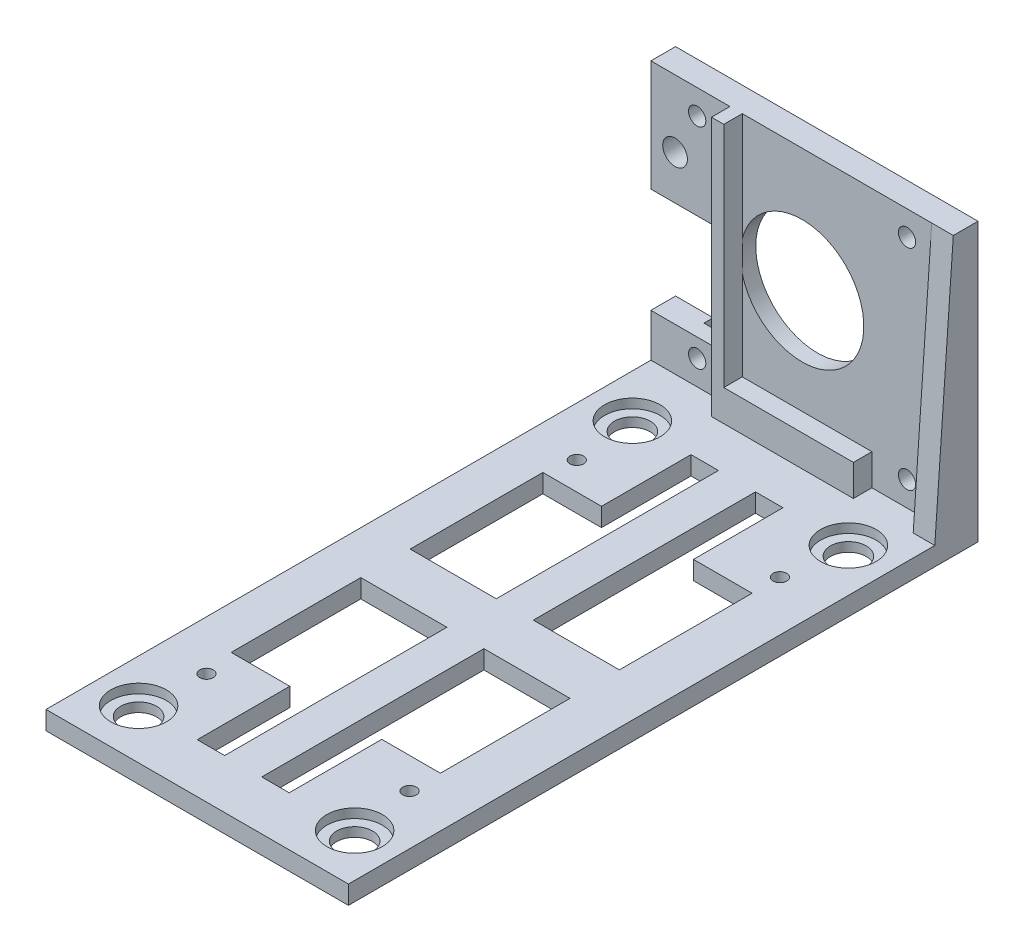
SolidWorks part; units mm, degrees
ref_plane "前视基准面" through (0, 0, 0) normal (0, 0, 1) x (1, 0, 0)
ref_plane "上视基准面" through (0, 0, 0) normal (0, 1, 0) x (1, 0, 0)
ref_plane "右视基准面" through (0, 0, 0) normal (1, 0, 0) x (0, 0, -1)
sketch "草图1" plane through (0, 0, 0) normal (0, 1, 0) x (1, 0, 0)
  line L0 (-35, 4) -> (-35, 25.5)
  line L1 (-1.1, 25.5) -> (-10.6, 25.5)
  line L2 (-10.6, 25.5) -> (-10.6, 40)
  line L3 (-21.05, 40) -> (-21.05, 4)
  line L4 (-1.1, 25.5) -> (-1.1, 4)
  line L5 (-1.1, -25) -> (-10.6, -25)
  line L6 (0, 40) -> (-1.1, 40)
  line L7 (-1.1, 40) -> (-1.1, 30) construction
  line L8 (-35, 40) -> (-34, 40)
  line L9 (-34, 40) -> (-34, 30) construction
  line L10 (-35, -40) -> (-34, -40)
  line L11 (-34, -40) -> (-34, -30) construction
  line L12 (0, -40) -> (-1.1, -40)
  line L13 (-1.1, -40) -> (-1.1, -30) construction
  line L14 (-10.6, -25) -> (-10.6, -40)
  line L15 (-21.05, 4) -> (-35, 4)
  line L16 (-1.1, -25) -> (-1.1, -4)
  line L17 (-42, -1) -> (-42, 46)
  line L18 (-42, -1) -> (-42, -48)
  line L19 (-42, -48) -> (0, -48)
  line L20 (0, -48) -> (7, -48)
  line L21 (-42, 46) -> (-42, 50)
  line L22 (7, -48) -> (7, 47)
  line L23 (-35, -4) -> (-35, -25)
  line L24 (-25.5, -25) -> (-35, -25)
  line L25 (-25.5, -40) -> (-25.5, -25)
  line L26 (-42, 50) -> (7, 50)
  line L27 (7, 50) -> (7, 47)
  line L29 (-15.05, 4) -> (-15.05, 40)
  line L30 (-25.5, 40) -> (-25.5, 25.5)
  line L32 (-25.5, 25.5) -> (-35, 25.5)
  line L33 (-21.05, 40) -> (-25.5, 40)
  line L34 (-15.05, 40) -> (-10.6, 40)
  line L35 (-15.05, 4) -> (-1.1, 4)
  line L36 (-21.05, -40) -> (-21.05, -4)
  line L37 (-21.05, -4) -> (-35, -4)
  line L38 (-25.5, -40) -> (-21.05, -40)
  line L39 (-15.05, -40) -> (-10.6, -40)
  line L40 (-15.05, -4) -> (-1.1, -4)
  line L41 (-15.05, -4) -> (-15.05, -40)
  circle A0 centre (-35, 40) radius 2.9
  circle A1 centre (0, 40) radius 2.9
  circle A2 centre (-35, -40) radius 2.9
  circle A3 centre (0, -40) radius 2.9
  circle A4 centre (-34, 30) radius 1.1
  circle A5 centre (-1.1, 30) radius 1.1
  circle A6 centre (-1.1, -30) radius 1.1
  circle A7 centre (-34, -30) radius 1.1
  point P50 (0, 0)
  point P53 (0, 0)
extrude "凸台-拉伸1" add sketch "草图1" along normal blind 3
sketch "草图2" plane through (0, 3, 0) normal (0, 1, 0) x (1, 0, 0)
  circle A0 centre (-35, 40) radius 4.5
  circle A1 centre (0, 40) radius 4.5
  circle A2 centre (0, -40) radius 4.5
  circle A3 centre (-35, -40) radius 4.5
extrude "切除-拉伸1" cut sketch "草图2" against normal blind 1.5
sketch "草图3" plane through (0, 3, 0) normal (0, 1, 0) x (1, 0, 0)
  line L0 (-42, 50) -> (-42, 54)
  line L1 (7, 50) -> (7, 54)
  line L2 (7, 54) -> (-42, 54)
  line L3 (-42, 50) -> (7, 50)
extrude "凸台-拉伸2" add sketch "草图3" along normal blind 42 and the other way blind 3
sketch "草图4" plane through (0, 0, -50) normal (0, 0, 1) x (1, 0, 0)
  line L0 (-17.5, 45) -> (-0.5, 45) construction
  line L1 (-42, 45) -> (7, 45) construction
  line L2 (-0.5, 45) -> (-0.5, 41) construction
  line L3 (-17.5, 45) -> (-34.5, 45) construction
  line L4 (-34.5, 45) -> (-34.5, 41) construction
  line L5 (-17.5, 45) -> (-17.5, 25)
  line L6 (-34.5, 7) -> (-0.5, 7) construction
  line L7 (-34.5, 7) -> (-29.5, 7)
  line L8 (-29.5, 7) -> (-29.5, 27)
  line L9 (-29.5, 27) -> (-42, 27)
  line L10 (-42, 3) -> (-42, 45) construction
  line L12 (-34.5, 7) -> (-34.5, 10)
  line L13 (-34.5, 41) -> (-34.5, 7) construction
  line L14 (-29.5, 10) -> (-41.9111, 10)
  line L15 (-42, 27) -> (-44.2605, 27)
  line L16 (-44.2605, 27) -> (-44.2605, 10)
  line L17 (-44.2605, 10) -> (-41.9111, 10)
  circle A0 centre (-34.5, 41) radius 1.4
  circle A1 centre (-0.5, 41) radius 1.4
  circle A2 centre (-34.5, 7) radius 1.4
  circle A3 centre (-0.5, 7) radius 1.4
  circle A4 centre (-17.5, 25) radius 10
  circle A5 centre (-38.08, 34.1308) radius 2
extrude "切除-拉伸2" cut sketch "草图4" against normal through all
sketch "草图5" plane through (0, 0, -54) normal (0, 0, -1) x (-1, 0, 0)
  line L0 (-0.7389, 41.652) -> (-0.7389, 42.3706)
  line L1 (-0.7389, 42.3706) -> (34.7855, 42.3706)
  line L2 (-0.7389, 41.652) -> (-0.7389, 4.8456)
  line L3 (0.0291, 5.6816) -> (-0.7389, 5.6816)
  line L4 (-0.7389, 5.6816) -> (34.9709, 5.6816)
  line L5 (35.9, 7) -> (35.9, 5.6816)
  line L6 (35.9, 5.6816) -> (34.9709, 5.6816)
  line L7 (35.9, 7) -> (35.9, 42.3706)
  line L8 (35.9, 42.3706) -> (34.7855, 42.3706)
  circle A0 centre (0.5, 41) radius 1.4 construction
  circle A1 centre (34.5, 41) radius 1.4 construction
  circle A2 centre (0.5, 7) radius 1.4 construction
  circle A3 centre (34.5, 7) radius 1.4 construction
  circle M1 centre (34.5, 41) radius 1.4
  circle M2 centre (0.5, 41) radius 1.4
  circle M3 centre (0.5, 7) radius 1.4
  line M4 (29.5, 27) -> (42, 27)
  line M10 (42, 10) -> (29.5, 10)
  line M11 (29.5, 10) -> (29.5, 27)
  circle M12 centre (34.5, 7) radius 1.4
  circle M13 centre (17.5, 25) radius 10
extrude "切除-拉伸3" cut sketch "草图5" against normal blind 1.5 contours L7 L1 L2 L4 M12 M10 M11 M4 M1 M2 M3 M13
sketch "草图7" plane through (7, 0, 0) normal (1, 0, 0) x (0, 0, -1)
  line L0 (50, 3) -> (47, 3)
  line L1 (50, 3) -> (-48, 3) construction
  line L2 (47, 3) -> (50, 45)
  line L3 (50, 45) -> (50, 3)
extrude "凸台-拉伸4" add sketch "草图7" against normal blind 3.5
sketch "草图9" plane through (0, 3, 0) normal (0, 1, 0) x (1, 0, 0)
  line L0 (-29.1887, 50) -> (-27.1887, 50)
  line L1 (-42, 50) -> (3.5, 50) construction
  line L2 (-29.1887, 50) -> (-29.1887, 47)
  line L3 (-29.1887, 47) -> (-27.1887, 47)
  line L4 (-27.1887, 50) -> (-27.1887, 47)
extrude "凸台-拉伸5" add sketch "草图9" along normal blind 42
sketch "草图10" plane through (-27.1887, 0, 0) normal (1, 0, 0) x (0, 0, -1)
  line L0 (50, 3) -> (50, 8.0666)
  line L1 (50, 22.5242) -> (50, 3) construction
  line L2 (50, 8.0666) -> (47, 8.0666)
  line L3 (47, 45) -> (47, 3) construction
  line L4 (47, 8.0666) -> (47, 3)
  line L5 (47, 3) -> (50, 3)
extrude "凸台-拉伸6" add sketch "草图10" along normal blind 21
